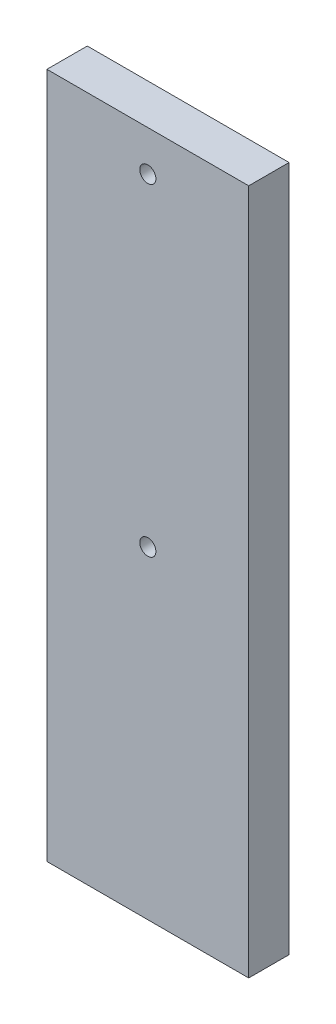
SolidWorks part; units mm, degrees
ref_plane "前视基准面" through (0, 0, 0) normal (0, 0, 1) x (1, 0, 0)
ref_plane "上视基准面" through (0, 0, 0) normal (0, 1, 0) x (1, 0, 0)
ref_plane "右视基准面" through (0, 0, 0) normal (1, 0, 0) x (0, 0, -1)
sketch "草图1" plane through (0, 0, 0) normal (0, 0, 1) x (1, 0, 0)
  line L0 (-29.7727, 40.5276) -> (20.2273, 40.5276)
  line L1 (20.2273, 40.5276) -> (20.2273, -129.4724)
  line L2 (20.2273, -129.4724) -> (-29.7727, -129.4724)
  line L3 (-29.7727, -129.4724) -> (-29.7727, 40.5276)
  line L4 (-4.7727, 40.5276) -> (-4.7727, -129.4724) construction
  line L5 (-4.7727, 40.5276) -> (-4.7727, 30.5276) construction
  line L6 (-4.7727, 30.5276) -> (-4.7727, -49.4724) construction
  circle A0 centre (-4.7727, 30.5276) radius 2
  circle A1 centre (-4.7727, -49.4724) radius 2
  dimension "D4" = 4
  dimension "D6" = 4
  dimension "D1" = 50
  dimension "D2" = 170
  dimension "D3" = 10
  dimension "D5" = 80
extrude "凸台-拉伸1" add sketch "草图1" along normal blind 10
